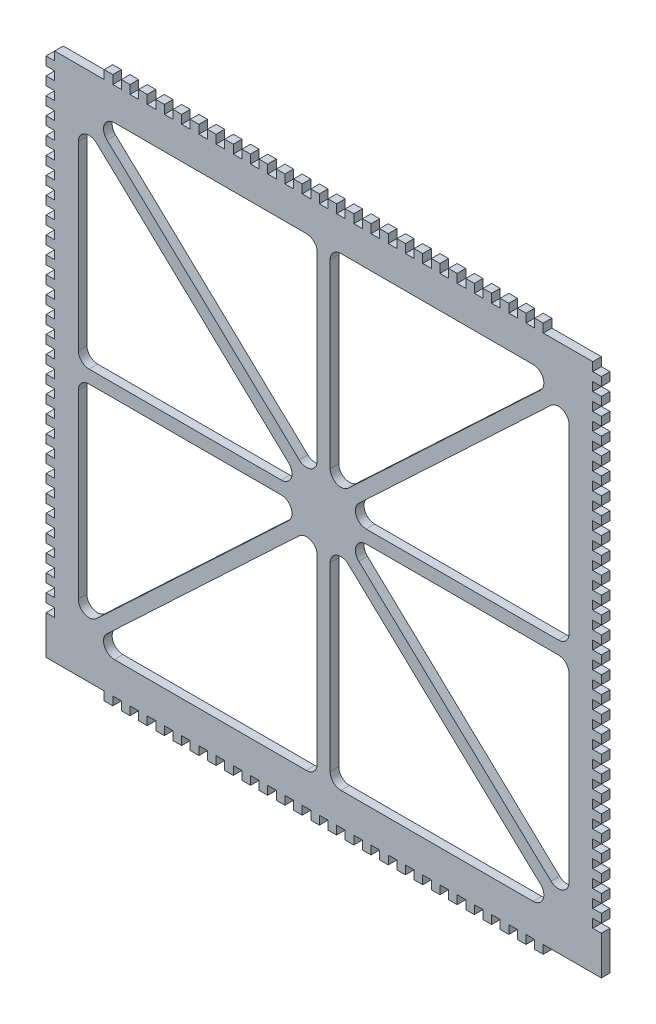
SolidWorks part; units mm, degrees
material "Cedar"
ref_plane "Front Plane" through (0, 0, 0) normal (0, 0, 1) x (1, 0, 0)
ref_plane "Top Plane" through (0, 0, 0) normal (0, 1, 0) x (1, 0, 0)
ref_plane "Right Plane" through (0, 0, 0) normal (1, 0, 0) x (0, 0, -1)
sketch "Sketch1" plane through (0, 0, 0) normal (0, 0, 1) x (1, 0, 0)
  line L0 (0, 0) -> (0, 50) construction
  line L1 (0, 0) -> (-64, 0) construction
  line L2 (-129, -123) -> (-129, 123)
  line L3 (-129, 123) -> (129, 123)
  line L5 (-97.2821, 108) -> (-8, 108)
  line L6 (5.0564, -5.1843) -> (7.1129, -3) construction
  line L7 (129, -123) -> (129, 123)
  line L8 (-129, -123) -> (129, -123)
  line L9 (3, -7.3686) -> (5.0564, -5.1843) construction
  line L10 (-105.5726, 95.6973) -> (-16.2905, 11.6405)
  line L11 (-19.7179, 3) -> (-109, 3)
  line L12 (8, 108) -> (97.2821, 108)
  line L13 (-100.7095, 99.3595) -> (-11.4274, 15.3027)
  line L14 (-3, 18.9432) -> (-3, 103)
  line L15 (65.2161, 57.7027) -> (61.1032, 62.0712) construction
  line L16 (3, 103) -> (3, 18.9432)
  line L17 (11.4274, 15.3027) -> (100.7095, 99.3595)
  line L18 (63.1597, 59.8869) -> (91.5544, 86.6198) construction
  line L19 (105.5726, 95.6973) -> (16.2905, 11.6405)
  line L20 (19.7179, 3) -> (109, 3)
  line L21 (109.8871, 108) -> (111.9436, 105.8157) construction
  line L22 (111.9436, 105.8157) -> (114, 103.6314) construction
  line L23 (-76.9918, 77.0299) -> (-81.1046, 72.6613) construction
  line L24 (-81.1046, 72.6613) -> (-79.0482, 74.8456) construction
  line L25 (-79.0482, 74.8456) -> (-91.6166, 86.6785) construction
  line L26 (-109.8871, 108) -> (-111.9436, 105.8157) construction
  line L27 (-111.9436, 105.8157) -> (-114, 103.6314) construction
  line L28 (9.2358, -9.119) -> (4.4502, -4.6135) construction
  line L29 (7.1793, -11.3033) -> (11.2922, -6.9347) construction
  line L30 (-5.0564, -5.1843) -> (-7.1129, -3) construction
  line L31 (-3, -7.3686) -> (-5.0564, -5.1843) construction
  line L32 (-10.2077, -10.0341) -> (-3.5943, -3.8077) construction
  line L33 (-12.2642, -7.8498) -> (-10.2077, -10.0341) construction
  line L34 (-8.1513, -12.2183) -> (-12.2642, -7.8498) construction
  line L35 (-111.9436, -105.8157) -> (-114, -103.6314) construction
  line L36 (-109.8871, -108) -> (-111.9436, -105.8157) construction
  line L37 (-81.1046, -72.6613) -> (-79.0482, -74.8456) construction
  line L38 (-76.9918, -77.0299) -> (-81.1046, -72.6613) construction
  line L39 (111.9436, -105.8157) -> (114, -103.6314) construction
  line L40 (109.8871, -108) -> (111.9436, -105.8157) construction
  line L41 (65.2161, -57.7027) -> (61.1032, -62.0712) construction
  line L42 (-114, -8) -> (-114, -92.0568)
  line L43 (114, -8) -> (114, -92.0568)
  line L44 (19.7179, -3) -> (109, -3)
  line L45 (105.5726, -95.6973) -> (16.2905, -11.6405)
  line L46 (114, 8) -> (114, 92.0568)
  line L47 (-114, 8) -> (-114, 92.0568)
  line L48 (-8.1513, 12.2183) -> (-12.2642, 7.8498) construction
  line L49 (-12.2642, 7.8498) -> (-10.2077, 10.0341) construction
  line L50 (-10.2077, 10.0341) -> (-3.5943, 3.8077) construction
  line L51 (-3, 7.3686) -> (-5.0564, 5.1843) construction
  line L52 (-5.0564, 5.1843) -> (-7.1129, 3) construction
  line L53 (7.1793, 11.3033) -> (11.2922, 6.9347) construction
  line L54 (9.2358, 9.119) -> (4.4502, 4.6135) construction
  line L55 (3, 7.3686) -> (5.0564, 5.1843) construction
  line L56 (5.0564, 5.1843) -> (7.1129, 3) construction
  line L57 (11.4274, -15.3027) -> (100.7095, -99.3595)
  line L58 (3, -103) -> (3, -18.9432)
  line L59 (-3, -18.9432) -> (-3, -103)
  line L60 (-100.7095, -99.3595) -> (-11.4274, -15.3027)
  line L61 (8, -108) -> (97.2821, -108)
  line L62 (-19.7179, -3) -> (-109, -3)
  line L63 (-105.5726, -95.6973) -> (-16.2905, -11.6405)
  line L64 (-97.2821, -108) -> (-8, -108)
  arc A0 (105.5726, 95.6973) -> (114, 92.0568) centre (109, 92.0568) cw
  arc A1 (109, 3) -> (114, 8) centre (109, 8) ccw
  arc A2 (16.2905, 11.6405) -> (19.7179, 3) centre (19.7179, 8) ccw
  arc A3 (3, 18.9432) -> (11.4274, 15.3027) centre (8, 18.9432) ccw
  arc A4 (100.7095, 99.3595) -> (97.2821, 108) centre (97.2821, 103) ccw
  arc A5 (3, 103) -> (8, 108) centre (8, 103) cw
  arc A6 (-100.7095, 99.3595) -> (-97.2821, 108) centre (-97.2821, 103) cw
  arc A7 (-11.4274, 15.3027) -> (-3, 18.9432) centre (-8, 18.9432) ccw
  arc A8 (-3, 103) -> (-8, 108) centre (-8, 103) ccw
  arc A9 (-16.2905, 11.6405) -> (-19.7179, 3) centre (-19.7179, 8) cw
  arc A10 (-114, 8) -> (-109, 3) centre (-109, 8) ccw
  arc A11 (-105.5726, 95.6973) -> (-114, 92.0568) centre (-109, 92.0568) ccw
  arc A12 (-105.5726, -95.6973) -> (-114, -92.0568) centre (-109, -92.0568) cw
  arc A13 (-114, -8) -> (-109, -3) centre (-109, -8) cw
  arc A14 (-16.2905, -11.6405) -> (-19.7179, -3) centre (-19.7179, -8) ccw
  arc A15 (-3, -103) -> (-8, -108) centre (-8, -103) cw
  arc A16 (-11.4274, -15.3027) -> (-3, -18.9432) centre (-8, -18.9432) cw
  arc A17 (-100.7095, -99.3595) -> (-97.2821, -108) centre (-97.2821, -103) ccw
  arc A18 (3, -103) -> (8, -108) centre (8, -103) ccw
  arc A19 (100.7095, -99.3595) -> (97.2821, -108) centre (97.2821, -103) cw
  arc A20 (3, -18.9432) -> (11.4274, -15.3027) centre (8, -18.9432) cw
  arc A21 (16.2905, -11.6405) -> (19.7179, -3) centre (19.7179, -8) cw
  arc A22 (109, -3) -> (114, -8) centre (109, -8) cw
  arc A23 (105.5726, -95.6973) -> (114, -92.0568) centre (109, -92.0568) ccw
  point P19 (0, 83)
  point P21 (0, 123)
  point P27 (-64, 0)
  point P28 (64, 0)
  point P29 (87, 0)
  point P34 (-87, 0)
  point P76 (114, 3)
  point P88 (3, 108)
  point P97 (-3, 108)
  point P103 (-114, 3)
  point P144 (-114, -3)
  point P145 (-3, -108)
  point P146 (3, -108)
  point P147 (114, -3)
  point P148 (0, -83)
  dimension "D3" = 15
  dimension "D8" = 123
  dimension "D7" = 6
  dimension "D9" = 6
  dimension "D10" = 3
  dimension "D11" = 123
  dimension "D12" = 5
  dimension "D2" = 258
  dimension "D4" = 15
  dimension "D5" = 3
  dimension "D6" = 3
  dimension "D13" = 15
extrude "Boss-Extrude1" add sketch "Sketch1" along normal blind 4
sketch "Sketch2" plane through (0, 0, 4) normal (0, 0, 1) x (1, 0, 0)
  line L0 (0, 0) -> (-89.2695, 0) construction
  line L1 (0, 0) -> (0, 71.1996) construction
  line L2 (-129, -33) -> (-125, -33)
  line L3 (-129, 123) -> (129, 123) construction
  line L4 (-129, -105) -> (-125, -105)
  line L5 (-129, 103) -> (-125, 103)
  line L6 (-129, 103) -> (-129, 107)
  line L7 (-129, 107) -> (-125, 107)
  line L8 (-125, 103) -> (-125, 107)
  line L9 (-129, 95) -> (-125, 95)
  line L10 (-129, 95) -> (-129, 99)
  line L11 (-129, 99) -> (-125, 99)
  line L12 (-125, 95) -> (-125, 99)
  line L13 (-129, 87) -> (-125, 87)
  line L14 (-129, 87) -> (-129, 91)
  line L15 (-129, 91) -> (-125, 91)
  line L16 (-125, 87) -> (-125, 91)
  line L17 (-129, 79) -> (-125, 79)
  line L18 (-129, 79) -> (-129, 83)
  line L19 (-129, 83) -> (-125, 83)
  line L20 (-125, 79) -> (-125, 83)
  line L21 (-129, 71) -> (-125, 71)
  line L22 (-129, 71) -> (-129, 75)
  line L23 (-129, 75) -> (-125, 75)
  line L24 (-125, 71) -> (-125, 75)
  line L25 (-129, 63) -> (-125, 63)
  line L26 (-129, 63) -> (-129, 67)
  line L27 (-129, 67) -> (-125, 67)
  line L28 (-125, 63) -> (-125, 67)
  line L29 (-129, 55) -> (-125, 55)
  line L30 (-129, 55) -> (-129, 59)
  line L31 (-129, 59) -> (-125, 59)
  line L32 (-125, 55) -> (-125, 59)
  line L33 (-129, 47) -> (-125, 47)
  line L34 (-129, 47) -> (-129, 51)
  line L35 (-129, 51) -> (-125, 51)
  line L36 (-125, 47) -> (-125, 51)
  line L37 (-129, 39) -> (-125, 39)
  line L38 (-129, 39) -> (-129, 43)
  line L39 (-129, 43) -> (-125, 43)
  line L40 (-125, 39) -> (-125, 43)
  line L41 (-129, 31) -> (-125, 31)
  line L42 (-129, 31) -> (-129, 35)
  line L43 (-129, 35) -> (-125, 35)
  line L44 (-125, 31) -> (-125, 35)
  line L45 (-129, 23) -> (-125, 23)
  line L46 (-129, 23) -> (-129, 27)
  line L47 (-129, 27) -> (-125, 27)
  line L48 (-125, 23) -> (-125, 27)
  line L49 (-129, 15) -> (-125, 15)
  line L50 (-129, 15) -> (-129, 19)
  line L51 (-129, 19) -> (-125, 19)
  line L52 (-125, 15) -> (-125, 19)
  line L53 (-129, 7) -> (-125, 7)
  line L54 (-129, 7) -> (-129, 11)
  line L55 (-129, 11) -> (-125, 11)
  line L56 (-125, 7) -> (-125, 11)
  line L57 (-129, -1) -> (-125, -1)
  line L58 (-129, -1) -> (-129, 3)
  line L59 (-129, 3) -> (-125, 3)
  line L60 (-125, -1) -> (-125, 3)
  line L61 (-129, -9) -> (-125, -9)
  line L62 (-129, -9) -> (-129, -5)
  line L63 (-129, -5) -> (-125, -5)
  line L64 (-125, -9) -> (-125, -5)
  line L65 (-129, -17) -> (-125, -17)
  line L66 (-129, -17) -> (-129, -13)
  line L67 (-129, -13) -> (-125, -13)
  line L68 (-125, -17) -> (-125, -13)
  line L69 (-129, -25) -> (-125, -25)
  line L70 (-129, -25) -> (-129, -21)
  line L71 (-129, -21) -> (-125, -21)
  line L72 (-125, -25) -> (-125, -21)
  line L74 (-129, 123) -> (-125, 123)
  line L75 (-129, 123) -> (-129, 119)
  line L76 (-129, 119) -> (-125, 119)
  line L77 (-125, 123) -> (-125, 119)
  line L78 (129, 123) -> (125, 123)
  line L79 (129, 123) -> (129, 119)
  line L80 (129, 119) -> (125, 119)
  line L81 (125, -105) -> (125, -101)
  line L82 (129, -101) -> (125, -101)
  line L83 (129, -105) -> (129, -101)
  line L84 (125, -97) -> (125, -93)
  line L85 (129, -93) -> (125, -93)
  line L86 (129, -97) -> (129, -93)
  line L87 (129, -97) -> (125, -97)
  line L88 (125, -89) -> (125, -85)
  line L89 (129, -85) -> (125, -85)
  line L90 (129, -89) -> (129, -85)
  line L91 (129, -89) -> (125, -89)
  line L92 (125, -81) -> (125, -77)
  line L93 (129, -77) -> (125, -77)
  line L94 (129, -81) -> (129, -77)
  line L95 (129, -81) -> (125, -81)
  line L96 (125, -73) -> (125, -69)
  line L97 (129, -69) -> (125, -69)
  line L98 (129, -73) -> (129, -69)
  line L99 (129, -73) -> (125, -73)
  line L100 (125, -65) -> (125, -61)
  line L101 (129, -61) -> (125, -61)
  line L102 (129, -65) -> (129, -61)
  line L103 (-129, 111) -> (-125, 111)
  line L104 (-129, 111) -> (-129, 115)
  line L105 (-129, 115) -> (-125, 115)
  line L106 (-125, 111) -> (-125, 115)
  line L107 (129, -65) -> (125, -65)
  line L108 (125, -57) -> (125, -53)
  line L109 (129, -53) -> (125, -53)
  line L110 (129, -57) -> (129, -53)
  line L111 (129, -57) -> (125, -57)
  line L112 (125, -49) -> (125, -45)
  line L113 (129, -45) -> (125, -45)
  line L114 (129, -49) -> (129, -45)
  line L115 (129, -49) -> (125, -49)
  line L116 (125, -41) -> (125, -37)
  line L117 (129, -37) -> (125, -37)
  line L118 (129, -41) -> (129, -37)
  line L119 (129, -41) -> (125, -41)
  line L120 (125, -33) -> (125, -29)
  line L121 (129, -29) -> (125, -29)
  line L122 (129, -33) -> (129, -29)
  line L123 (125, 111) -> (125, 115)
  line L124 (129, 115) -> (125, 115)
  line L125 (129, 111) -> (129, 115)
  line L126 (129, 111) -> (125, 111)
  line L127 (125, -25) -> (125, -21)
  line L128 (129, -21) -> (125, -21)
  line L129 (129, -25) -> (129, -21)
  line L130 (129, -25) -> (125, -25)
  line L131 (-129, -33) -> (-129, -29)
  line L132 (125, -17) -> (125, -13)
  line L133 (129, -13) -> (125, -13)
  line L134 (129, -17) -> (129, -13)
  line L135 (129, -17) -> (125, -17)
  line L136 (125, -9) -> (125, -5)
  line L137 (129, -5) -> (125, -5)
  line L138 (129, -9) -> (129, -5)
  line L139 (129, -9) -> (125, -9)
  line L140 (125, -1) -> (125, 3)
  line L141 (129, 3) -> (125, 3)
  line L142 (129, -1) -> (129, 3)
  line L143 (129, -1) -> (125, -1)
  line L144 (125, 7) -> (125, 11)
  line L145 (129, 11) -> (125, 11)
  line L146 (129, 7) -> (129, 11)
  line L147 (129, 7) -> (125, 7)
  line L148 (125, 15) -> (125, 19)
  line L149 (129, 19) -> (125, 19)
  line L150 (-129, -29) -> (-125, -29)
  line L151 (-125, -33) -> (-125, -29)
  line L152 (-129, -41) -> (-125, -41)
  line L153 (-129, -41) -> (-129, -37)
  line L154 (-129, -37) -> (-125, -37)
  line L155 (-125, -41) -> (-125, -37)
  line L156 (-129, -49) -> (-125, -49)
  line L157 (-129, -49) -> (-129, -45)
  line L158 (-129, -45) -> (-125, -45)
  line L159 (-125, -49) -> (-125, -45)
  line L160 (-129, -57) -> (-125, -57)
  line L161 (-129, -57) -> (-129, -53)
  line L162 (-129, -53) -> (-125, -53)
  line L163 (-125, -57) -> (-125, -53)
  line L164 (-129, -65) -> (-125, -65)
  line L165 (-129, -65) -> (-129, -61)
  line L166 (-129, -61) -> (-125, -61)
  line L167 (-125, -65) -> (-125, -61)
  line L168 (-129, -73) -> (-125, -73)
  line L169 (-129, -73) -> (-129, -69)
  line L170 (-129, -69) -> (-125, -69)
  line L171 (-125, -73) -> (-125, -69)
  line L172 (129, 15) -> (129, 19)
  line L173 (129, 15) -> (125, 15)
  line L174 (125, 23) -> (125, 27)
  line L175 (129, 27) -> (125, 27)
  line L176 (129, 23) -> (129, 27)
  line L177 (129, 23) -> (125, 23)
  line L178 (125, 31) -> (125, 35)
  line L179 (129, 35) -> (125, 35)
  line L180 (129, 31) -> (129, 35)
  line L181 (129, 31) -> (125, 31)
  line L182 (125, 39) -> (125, 43)
  line L183 (129, 43) -> (125, 43)
  line L184 (129, 39) -> (129, 43)
  line L185 (129, 39) -> (125, 39)
  line L186 (125, 47) -> (125, 51)
  line L187 (129, 51) -> (125, 51)
  line L188 (129, 47) -> (129, 51)
  line L189 (129, 47) -> (125, 47)
  line L190 (125, 55) -> (125, 59)
  line L191 (129, 59) -> (125, 59)
  line L192 (129, 55) -> (129, 59)
  line L193 (129, 55) -> (125, 55)
  line L194 (125, 63) -> (125, 67)
  line L195 (129, 67) -> (125, 67)
  line L196 (-129, -81) -> (-125, -81)
  line L197 (-129, -81) -> (-129, -77)
  line L198 (-129, -77) -> (-125, -77)
  line L199 (-125, -81) -> (-125, -77)
  line L200 (-129, -89) -> (-125, -89)
  line L201 (-129, -89) -> (-129, -85)
  line L202 (-129, -85) -> (-125, -85)
  line L203 (-125, -89) -> (-125, -85)
  line L204 (-129, -97) -> (-125, -97)
  line L205 (-129, -97) -> (-129, -93)
  line L206 (-129, -93) -> (-125, -93)
  line L207 (-125, -97) -> (-125, -93)
  line L208 (129, 63) -> (129, 67)
  line L209 (129, 63) -> (125, 63)
  line L210 (125, 71) -> (125, 75)
  line L211 (129, 75) -> (125, 75)
  line L212 (129, 71) -> (129, 75)
  line L213 (129, 71) -> (125, 71)
  line L214 (125, 79) -> (125, 83)
  line L215 (129, 83) -> (125, 83)
  line L216 (129, 79) -> (129, 83)
  line L217 (129, 79) -> (125, 79)
  line L218 (125, 87) -> (125, 91)
  line L219 (129, 91) -> (125, 91)
  line L220 (125, 123) -> (125, 119)
  line L221 (-129, -105) -> (-129, -101)
  line L222 (-129, -101) -> (-125, -101)
  line L223 (-125, -105) -> (-125, -101)
  line L232 (129, 87) -> (129, 91)
  line L233 (129, 87) -> (125, 87)
  line L234 (125, 95) -> (125, 99)
  line L235 (129, 99) -> (125, 99)
  line L236 (129, 95) -> (129, 99)
  line L237 (129, 95) -> (125, 95)
  line L238 (125, 103) -> (125, 107)
  line L239 (129, 107) -> (125, 107)
  line L240 (129, 103) -> (129, 107)
  line L241 (129, 103) -> (125, 103)
  line L242 (129, -105) -> (125, -105)
  line L243 (129, -33) -> (125, -33)
  line L244 (-129, -123) -> (-129, 123) construction
  dimension "D1" = 8
  dimension "D2" = 4
  dimension "D3" = 4
  dimension "D4" = 28
  dimension "D5" = 4
  dimension "D6" = 4
  dimension "D7" = 4
extrude "Cut-Extrude1" cut sketch "Sketch2" against normal blind 4
sketch "Sketch3" plane through (0, 0, 4) normal (0, 0, 1) x (1, 0, 0)
  line L0 (0, 123) -> (0, 91.9358) construction
  line L1 (0, 0) -> (-94.9533, 0) construction
  line L2 (-129, 123) -> (129, 123) construction
  line L3 (-2, 123) -> (-6, 123)
  line L4 (-2, 123) -> (-2, 127)
  line L5 (-2, 127) -> (-6, 127)
  line L6 (-6, 123) -> (-6, 127)
  line L7 (-10, 123) -> (-14, 123)
  line L8 (-10, 123) -> (-10, 127)
  line L9 (-10, 127) -> (-14, 127)
  line L10 (-14, 123) -> (-14, 127)
  line L11 (-18, 123) -> (-22, 123)
  line L12 (-18, 123) -> (-18, 127)
  line L13 (-18, 127) -> (-22, 127)
  line L14 (-22, 123) -> (-22, 127)
  line L15 (-26, 123) -> (-30, 123)
  line L16 (-26, 123) -> (-26, 127)
  line L17 (-26, 127) -> (-30, 127)
  line L18 (-30, 123) -> (-30, 127)
  line L19 (-34, 123) -> (-38, 123)
  line L20 (-34, 123) -> (-34, 127)
  line L21 (-34, 127) -> (-38, 127)
  line L22 (-38, 123) -> (-38, 127)
  line L23 (-42, 123) -> (-46, 123)
  line L24 (-42, 123) -> (-42, 127)
  line L25 (-42, 127) -> (-46, 127)
  line L26 (-46, 123) -> (-46, 127)
  line L27 (-50, 123) -> (-54, 123)
  line L28 (-50, 123) -> (-50, 127)
  line L29 (-50, 127) -> (-54, 127)
  line L30 (-54, 123) -> (-54, 127)
  line L31 (-58, 123) -> (-62, 123)
  line L32 (-58, 123) -> (-58, 127)
  line L33 (-58, 127) -> (-62, 127)
  line L34 (-62, 123) -> (-62, 127)
  line L35 (-66, 123) -> (-70, 123)
  line L36 (-66, 123) -> (-66, 127)
  line L37 (-66, 127) -> (-70, 127)
  line L38 (-70, 123) -> (-70, 127)
  line L39 (-74, 123) -> (-78, 123)
  line L40 (-74, 123) -> (-74, 127)
  line L41 (-74, 127) -> (-78, 127)
  line L42 (-78, 123) -> (-78, 127)
  line L43 (-82, 123) -> (-86, 123)
  line L44 (-82, 123) -> (-82, 127)
  line L45 (-82, 127) -> (-86, 127)
  line L46 (-86, 123) -> (-86, 127)
  line L47 (-90, 123) -> (-94, 123)
  line L48 (-90, 123) -> (-90, 127)
  line L49 (-90, 127) -> (-94, 127)
  line L50 (-94, 123) -> (-94, 127)
  line L51 (-98, 123) -> (-102, 123)
  line L52 (-98, 123) -> (-98, 127)
  line L53 (-98, 127) -> (-102, 127)
  line L54 (-102, 123) -> (-102, 127)
  line L55 (102, 123) -> (102, 127)
  line L56 (98, 127) -> (102, 127)
  line L57 (98, 123) -> (98, 127)
  line L58 (98, 123) -> (102, 123)
  line L59 (94, 123) -> (94, 127)
  line L60 (90, 127) -> (94, 127)
  line L61 (90, 123) -> (90, 127)
  line L62 (90, 123) -> (94, 123)
  line L63 (86, 123) -> (86, 127)
  line L64 (82, 127) -> (86, 127)
  line L65 (82, 123) -> (82, 127)
  line L66 (82, 123) -> (86, 123)
  line L67 (78, 123) -> (78, 127)
  line L68 (74, 127) -> (78, 127)
  line L69 (74, 123) -> (74, 127)
  line L70 (74, 123) -> (78, 123)
  line L71 (70, 123) -> (70, 127)
  line L72 (66, 127) -> (70, 127)
  line L73 (66, 123) -> (66, 127)
  line L74 (66, 123) -> (70, 123)
  line L75 (62, 123) -> (62, 127)
  line L76 (58, 127) -> (62, 127)
  line L77 (58, 123) -> (58, 127)
  line L78 (58, 123) -> (62, 123)
  line L79 (54, 123) -> (54, 127)
  line L80 (50, 127) -> (54, 127)
  line L81 (50, 123) -> (50, 127)
  line L82 (50, 123) -> (54, 123)
  line L83 (46, 123) -> (46, 127)
  line L84 (42, 127) -> (46, 127)
  line L85 (42, 123) -> (42, 127)
  line L86 (42, 123) -> (46, 123)
  line L87 (38, 123) -> (38, 127)
  line L88 (34, 127) -> (38, 127)
  line L89 (34, 123) -> (34, 127)
  line L90 (34, 123) -> (38, 123)
  line L91 (30, 123) -> (30, 127)
  line L92 (26, 127) -> (30, 127)
  line L93 (26, 123) -> (26, 127)
  line L94 (26, 123) -> (30, 123)
  line L95 (22, 123) -> (22, 127)
  line L96 (18, 127) -> (22, 127)
  line L97 (18, 123) -> (18, 127)
  line L98 (18, 123) -> (22, 123)
  line L99 (14, 123) -> (14, 127)
  line L100 (10, 127) -> (14, 127)
  line L101 (10, 123) -> (10, 127)
  line L102 (10, 123) -> (14, 123)
  line L103 (6, 123) -> (6, 127)
  line L104 (2, 127) -> (6, 127)
  line L105 (2, 123) -> (2, 127)
  line L106 (2, 123) -> (6, 123)
  line L107 (2, -123) -> (6, -123)
  line L108 (2, -123) -> (2, -127)
  line L109 (2, -127) -> (6, -127)
  line L110 (6, -123) -> (6, -127)
  line L111 (10, -123) -> (14, -123)
  line L112 (10, -123) -> (10, -127)
  line L113 (10, -127) -> (14, -127)
  line L114 (14, -123) -> (14, -127)
  line L115 (18, -123) -> (22, -123)
  line L116 (18, -123) -> (18, -127)
  line L117 (18, -127) -> (22, -127)
  line L118 (22, -123) -> (22, -127)
  line L119 (26, -123) -> (30, -123)
  line L120 (26, -123) -> (26, -127)
  line L121 (26, -127) -> (30, -127)
  line L122 (30, -123) -> (30, -127)
  line L123 (34, -123) -> (38, -123)
  line L124 (34, -123) -> (34, -127)
  line L125 (34, -127) -> (38, -127)
  line L126 (38, -123) -> (38, -127)
  line L127 (42, -123) -> (46, -123)
  line L128 (42, -123) -> (42, -127)
  line L129 (42, -127) -> (46, -127)
  line L130 (46, -123) -> (46, -127)
  line L131 (50, -123) -> (54, -123)
  line L132 (50, -123) -> (50, -127)
  line L133 (50, -127) -> (54, -127)
  line L134 (54, -123) -> (54, -127)
  line L135 (58, -123) -> (62, -123)
  line L136 (58, -123) -> (58, -127)
  line L137 (58, -127) -> (62, -127)
  line L138 (62, -123) -> (62, -127)
  line L139 (66, -123) -> (70, -123)
  line L140 (66, -123) -> (66, -127)
  line L141 (66, -127) -> (70, -127)
  line L142 (70, -123) -> (70, -127)
  line L143 (74, -123) -> (78, -123)
  line L144 (74, -123) -> (74, -127)
  line L145 (74, -127) -> (78, -127)
  line L146 (78, -123) -> (78, -127)
  line L147 (82, -123) -> (86, -123)
  line L148 (82, -123) -> (82, -127)
  line L149 (82, -127) -> (86, -127)
  line L150 (86, -123) -> (86, -127)
  line L151 (90, -123) -> (94, -123)
  line L152 (90, -123) -> (90, -127)
  line L153 (90, -127) -> (94, -127)
  line L154 (94, -123) -> (94, -127)
  line L155 (98, -123) -> (102, -123)
  line L156 (98, -123) -> (98, -127)
  line L157 (98, -127) -> (102, -127)
  line L158 (102, -123) -> (102, -127)
  line L159 (-102, -123) -> (-102, -127)
  line L160 (-98, -127) -> (-102, -127)
  line L161 (-98, -123) -> (-98, -127)
  line L162 (-98, -123) -> (-102, -123)
  line L163 (-94, -123) -> (-94, -127)
  line L164 (-90, -127) -> (-94, -127)
  line L165 (-90, -123) -> (-90, -127)
  line L166 (-90, -123) -> (-94, -123)
  line L167 (-86, -123) -> (-86, -127)
  line L168 (-82, -127) -> (-86, -127)
  line L169 (-82, -123) -> (-82, -127)
  line L170 (-82, -123) -> (-86, -123)
  line L171 (-78, -123) -> (-78, -127)
  line L172 (-74, -127) -> (-78, -127)
  line L173 (-74, -123) -> (-74, -127)
  line L174 (-74, -123) -> (-78, -123)
  line L175 (-70, -123) -> (-70, -127)
  line L176 (-66, -127) -> (-70, -127)
  line L177 (-66, -123) -> (-66, -127)
  line L178 (-66, -123) -> (-70, -123)
  line L179 (-62, -123) -> (-62, -127)
  line L180 (-58, -127) -> (-62, -127)
  line L181 (-58, -123) -> (-58, -127)
  line L182 (-58, -123) -> (-62, -123)
  line L183 (-54, -123) -> (-54, -127)
  line L184 (-50, -127) -> (-54, -127)
  line L185 (-50, -123) -> (-50, -127)
  line L186 (-50, -123) -> (-54, -123)
  line L187 (-46, -123) -> (-46, -127)
  line L188 (-42, -127) -> (-46, -127)
  line L189 (-42, -123) -> (-42, -127)
  line L190 (-42, -123) -> (-46, -123)
  line L191 (-38, -123) -> (-38, -127)
  line L192 (-34, -127) -> (-38, -127)
  line L193 (-34, -123) -> (-34, -127)
  line L194 (-34, -123) -> (-38, -123)
  line L195 (-30, -123) -> (-30, -127)
  line L196 (-26, -127) -> (-30, -127)
  line L197 (-26, -123) -> (-26, -127)
  line L198 (-26, -123) -> (-30, -123)
  line L199 (-22, -123) -> (-22, -127)
  line L200 (-18, -127) -> (-22, -127)
  line L201 (-18, -123) -> (-18, -127)
  line L202 (-18, -123) -> (-22, -123)
  line L203 (-14, -123) -> (-14, -127)
  line L204 (-10, -127) -> (-14, -127)
  line L205 (-10, -123) -> (-10, -127)
  line L206 (-10, -123) -> (-14, -123)
  line L207 (-6, -123) -> (-6, -127)
  line L208 (-2, -127) -> (-6, -127)
  line L209 (-2, -123) -> (-2, -127)
  line L210 (-2, -123) -> (-6, -123)
  dimension "D1" = 4
  dimension "D2" = 4
  dimension "D3" = 2
  dimension "D4" = 13
extrude "Boss-Extrude2" add sketch "Sketch3" against normal blind 4
